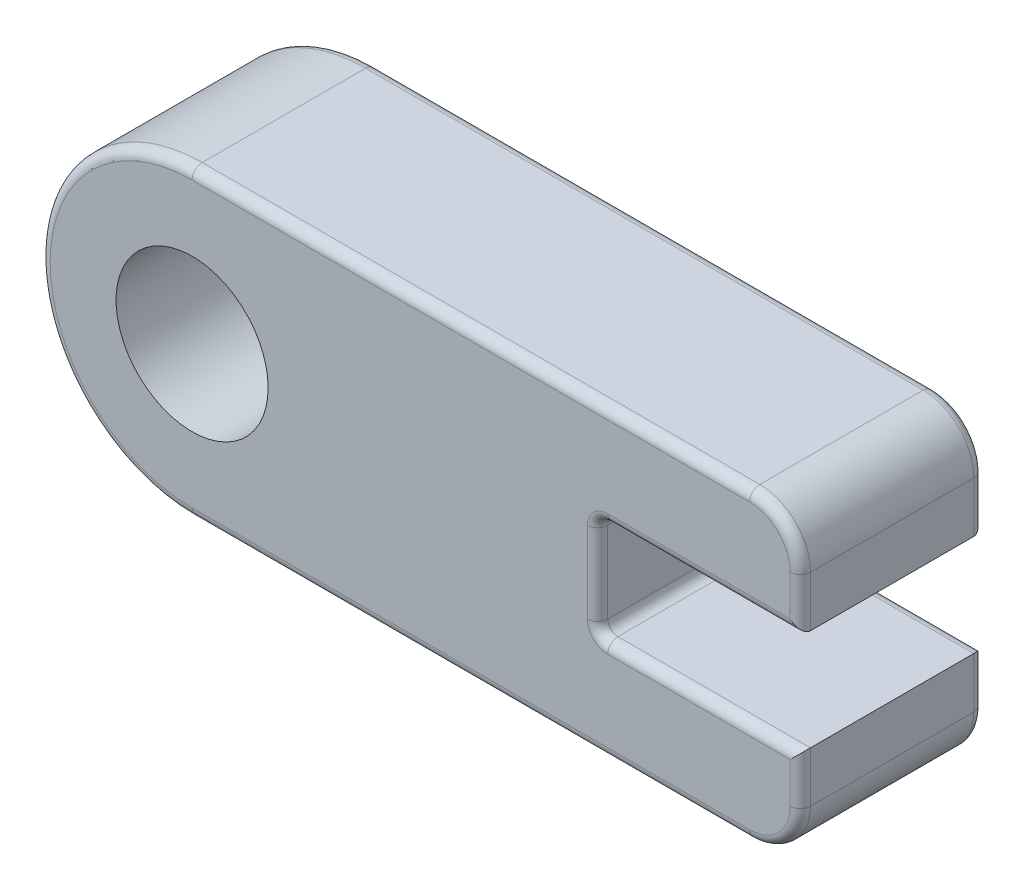
SolidWorks part; units mm, degrees
ref_plane "Front Plane" through (0, 0, 0) normal (0, 0, 1) x (1, 0, 0)
ref_plane "Top Plane" through (0, 0, 0) normal (0, 1, 0) x (1, 0, 0)
ref_plane "Right Plane" through (0, 0, 0) normal (1, 0, 0) x (0, 0, -1)
sketch "Sketch1" plane through (0, 0, 0) normal (0, 0, 1) x (1, 0, 0)
  line L0 (101.6, 12.7) -> (50.8, 12.7)
  line L1 (-50.8, 38.1) -> (101.6, 38.1)
  line L2 (101.6, 38.1) -> (101.6, 12.7)
  line L3 (101.6, -38.1) -> (-50.8, -38.1)
  line L4 (50.8, 12.7) -> (50.8, -12.7)
  line L5 (50.8, -12.7) -> (101.6, -12.7)
  line L6 (101.6, -12.7) -> (101.6, -38.1)
  arc A0 (-50.8, 38.1) -> (-50.8, -38.1) centre (-50.8, 0) ccw
  circle A1 centre (-50.8, 0) radius 19.05
  dimension "D2" = 38.1
  dimension "D9" = 38.1
  dimension "D1" = 152.4
  dimension "D3" = 76.2
  dimension "D4" = 25.4
  dimension "D5" = 25.4
  dimension "D6" = 50.8
  dimension "D7" = 50.8
  dimension "D8" = 12.7
extrude "Boss-Extrude1" add sketch "Sketch1" along normal blind 46.0016
fillet "Fillet1" radius 12.7 2 edges at (101.6, -38.1, 23.0008) (101.6, 38.1, 23.0008)
fillet "Fillet2" radius 2.54 22 edges at (76.2, -12.7, 0) (76.2, 12.7, 0) (76.2, -12.7, 46.0016) (76.2, 12.7, 46.0016) (101.6, 19.05, 46.0016) (97.8803, 34.3803, 46.0016) (101.6, -19.05, 46.0016) (97.8803, -34.3803, 46.0016) (19.05, -38.1, 46.0016) (-88.9, 0, 46.0016) (101.6, -19.05, 0) (97.8803, -34.3803, 0) (19.05, -38.1, 0) (-88.9, 0, 0) (19.05, 38.1, 0) (101.6, 19.05, 0) (19.05, 38.1, 46.0016) (97.8803, 34.3803, 0) (50.8, 0, 0) (50.8, 0, 46.0016) (50.8, -12.7, 23.0008) (50.8, 12.7, 23.0008)
